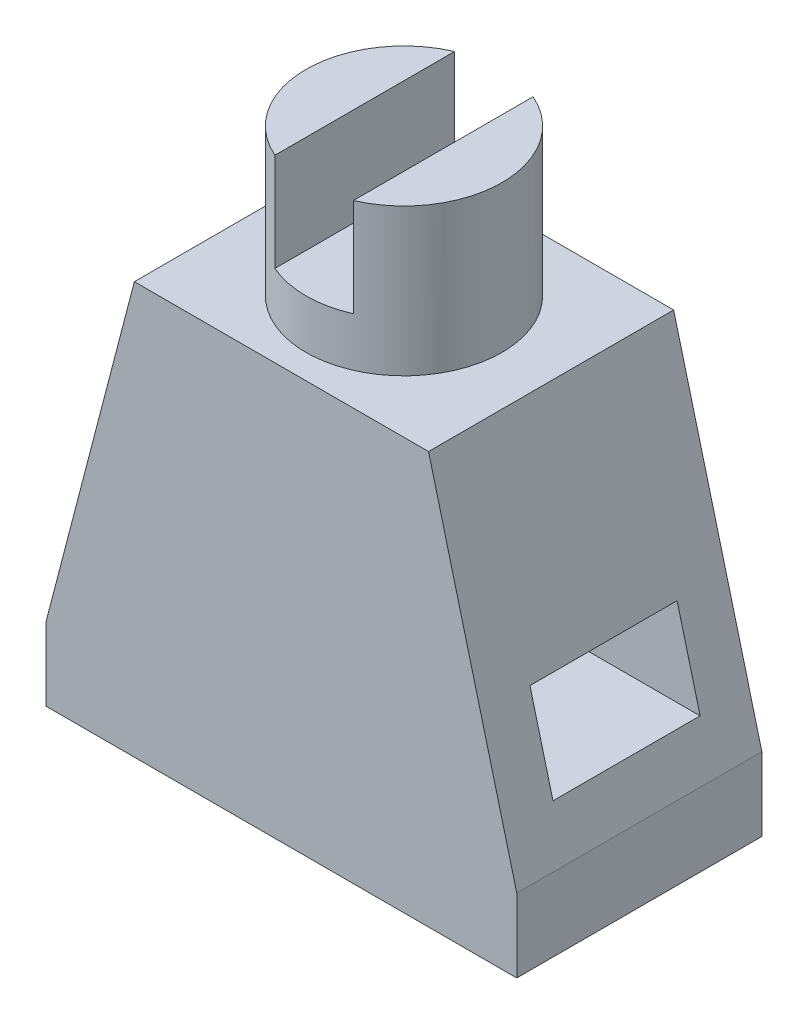
SolidWorks part; units mm, degrees
ref_plane "Front Plane" through (0, 0, 0) normal (0, 0, 1) x (1, 0, 0)
ref_plane "Top Plane" through (0, 0, 0) normal (0, 1, 0) x (1, 0, 0)
ref_plane "Right Plane" through (0, 0, 0) normal (1, 0, 0) x (0, 0, -1)
sketch "Sketch1" plane through (0, 0, 0) normal (0, 1, 0) x (1, 0, 0)
  line L1 (0, 0) -> (96, 0)
  line L2 (0, 0) -> (0, 50)
  line L3 (0, 50) -> (96, 50)
  line L4 (96, 0) -> (96, 50)
  dimension "D1" = 96
  dimension "D2" = 50
extrude "Boss-Extrude1" add sketch "Sketch1" along normal blind 84
sketch "Sketch5" plane through (0, 0, 0) normal (-1, 0, 0) x (0, 0, 1)
  line L0 (-50, 0) -> (0, 0) construction
  line L1 (-40, 25) -> (-10, 25)
  line L2 (-40, 25) -> (-40, 43)
  line L3 (-40, 43) -> (-10, 43)
  line L4 (-10, 25) -> (-10, 43)
  line L5 (0, 84) -> (0, 0) construction
  dimension "D1" = 30
  dimension "D2" = 25
  dimension "D3" = 10
  dimension "D4" = 18
extrude "Cut-Extrude2" cut sketch "Sketch5" against normal blind 102
ref_plane "Plane2" through (48, 0, 0) normal (-1, 0, 0) x (0, 0, 1)
sketch "Sketch2" plane through (0, 0, 0) normal (0, 0, 1) x (1, 0, 0)
  line L0 (0, 84) -> (96, 84) construction
  line L1 (0, 84) -> (0, 0) construction
  line L2 (0, 15) -> (18, 84)
  point P0 (18, 84)
  point P1 (0, 15)
  dimension "D1" = 15
extrude "Cut-Extrude1" cut sketch "Sketch2" against normal through all and the other way through all
mirror "Mirror1" about plane through (48, 0, 0) normal (-1, 0, 0) of "Cut-Extrude1"
sketch "Sketch6" plane through (0, 84, 0) normal (0, 1, 0) x (1, 0, 0)
  circle A0 centre (48, 25) radius 20
  point P3 (68, 25)
  point P4 (48, 45)
  dimension "D1" = 40
extrude "Boss-Extrude2" add sketch "Sketch6" along normal blind 30
sketch "Sketch8" plane through (0, 114, 0) normal (0, 1, 0) x (1, 0, 0)
  line L0 (40, 6.6697) -> (40, 43.3303)
  line L3 (56, 6.6697) -> (56, 43.3303)
  circle A0 centre (48, 25) radius 20 construction
  circle A1 centre (48, 25) radius 20 construction
  arc A2 (40, 6.6697) -> (56, 6.6697) centre (48, 25) ccw
  arc A3 (56, 43.3303) -> (40, 43.3303) centre (48, 25) ccw
  dimension "D1" = 16
extrude "Cut-Extrude3" cut sketch "Sketch8" against normal blind 20
